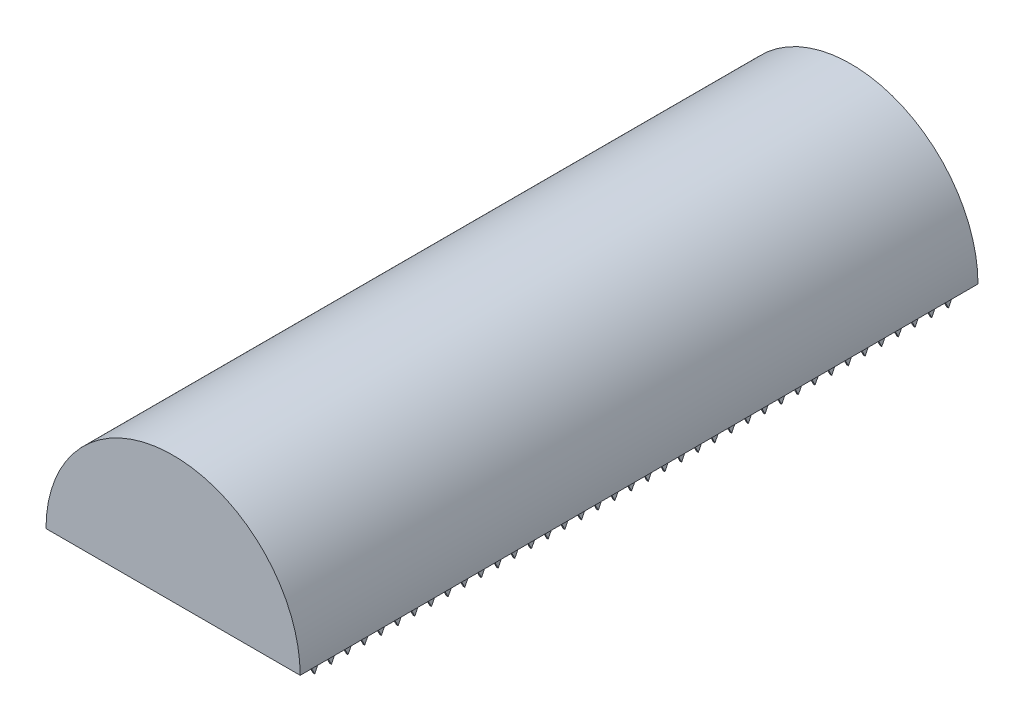
SolidWorks part; units mm, degrees
ref_plane "Front Plane" through (0, 0, 0) normal (0, 0, 1) x (1, 0, 0)
ref_plane "Top Plane" through (0, 0, 0) normal (0, 1, 0) x (1, 0, 0)
ref_plane "Right Plane" through (0, 0, 0) normal (1, 0, 0) x (0, 0, -1)
sketch "Sketch1" plane through (0, 0, 0) normal (0, 0, 1) x (1, 0, 0)
  line L0 (-76.2, 0) -> (76.2, 0)
  arc A0 (-76.2, 0) -> (76.2, 0) centre (0, 0) cw
  dimension "D1" = 76.2
extrude "Boss-Extrude1" add sketch "Sketch1" along normal blind 406.4
shell "Shell1" thickness 6.35
ref_plane "Plane1" through (69.85, 0, 0) normal (1, 0, 0) x (0, 0, -1)
sketch "Sketch3" plane through (69.85, 0, 0) normal (1, 0, 0) x (0, 0, -1)
  line L0 (-6.35, 0) -> (-11.35, -10)
  line L1 (-11.35, -10) -> (-16.35, 0)
  line L2 (-400.05, 0) -> (-6.35, 0) construction
  line L3 (-11.35, -10) -> (-11.35, 0) construction
  line L4 (-6.35, 0) -> (-16.35, 0) construction
  line L5 (-16.35, 0) -> (-21.35, -10)
  line L6 (-21.35, -10) -> (-26.35, 0)
  line L7 (-16.35, 0) -> (-26.35, 0) construction
  line L8 (-26.35, 0) -> (-31.35, -10)
  line L9 (-31.35, -10) -> (-36.35, 0)
  line L10 (-26.35, 0) -> (-36.35, 0) construction
  line L11 (-36.35, 0) -> (-41.35, -10)
  line L12 (-41.35, -10) -> (-46.35, 0)
  line L13 (-36.35, 0) -> (-46.35, 0) construction
  line L14 (-46.35, 0) -> (-51.35, -10)
  line L15 (-51.35, -10) -> (-56.35, 0)
  line L16 (-46.35, 0) -> (-56.35, 0) construction
  line L17 (-56.35, 0) -> (-61.35, -10)
  line L18 (-61.35, -10) -> (-66.35, 0)
  line L19 (-56.35, 0) -> (-66.35, 0) construction
  line L20 (-66.35, 0) -> (-71.35, -10)
  line L21 (-71.35, -10) -> (-76.35, 0)
  line L22 (-66.35, 0) -> (-76.35, 0) construction
  line L23 (-76.35, 0) -> (-81.35, -10)
  line L24 (-81.35, -10) -> (-86.35, 0)
  line L25 (-76.35, 0) -> (-86.35, 0) construction
  line L26 (-86.35, 0) -> (-91.35, -10)
  line L27 (-91.35, -10) -> (-96.35, 0)
  line L28 (-86.35, 0) -> (-96.35, 0) construction
  line L29 (-96.35, 0) -> (-101.35, -10)
  line L30 (-101.35, -10) -> (-106.35, 0)
  line L31 (-96.35, 0) -> (-106.35, 0) construction
  line L32 (-106.35, 0) -> (-111.35, -10)
  line L33 (-111.35, -10) -> (-116.35, 0)
  line L34 (-106.35, 0) -> (-116.35, 0) construction
  line L35 (-116.35, 0) -> (-121.35, -10)
  line L36 (-121.35, -10) -> (-126.35, 0)
  line L37 (-116.35, 0) -> (-126.35, 0) construction
  line L38 (-126.35, 0) -> (-131.35, -10)
  line L39 (-131.35, -10) -> (-136.35, 0)
  line L40 (-126.35, 0) -> (-136.35, 0) construction
  line L41 (-136.35, 0) -> (-141.35, -10)
  line L42 (-141.35, -10) -> (-146.35, 0)
  line L43 (-136.35, 0) -> (-146.35, 0) construction
  line L44 (-146.35, 0) -> (-151.35, -10)
  line L45 (-151.35, -10) -> (-156.35, 0)
  line L46 (-146.35, 0) -> (-156.35, 0) construction
  line L47 (-156.35, 0) -> (-161.35, -10)
  line L48 (-161.35, -10) -> (-166.35, 0)
  line L49 (-156.35, 0) -> (-166.35, 0) construction
  line L50 (-166.35, 0) -> (-171.35, -10)
  line L51 (-171.35, -10) -> (-176.35, 0)
  line L52 (-166.35, 0) -> (-176.35, 0) construction
  line L53 (-176.35, 0) -> (-181.35, -10)
  line L54 (-181.35, -10) -> (-186.35, 0)
  line L55 (-176.35, 0) -> (-186.35, 0) construction
  line L56 (-186.35, 0) -> (-191.35, -10)
  line L57 (-191.35, -10) -> (-196.35, 0)
  line L58 (-186.35, 0) -> (-196.35, 0) construction
  line L59 (-196.35, 0) -> (-201.35, -10)
  line L60 (-201.35, -10) -> (-206.35, 0)
  line L61 (-196.35, 0) -> (-206.35, 0) construction
  line L62 (-206.35, 0) -> (-211.35, -10)
  line L63 (-211.35, -10) -> (-216.35, 0)
  line L64 (-206.35, 0) -> (-216.35, 0) construction
  line L65 (-216.35, 0) -> (-221.35, -10)
  line L66 (-221.35, -10) -> (-226.35, 0)
  line L67 (-216.35, 0) -> (-226.35, 0) construction
  line L68 (-226.35, 0) -> (-231.35, -10)
  line L69 (-231.35, -10) -> (-236.35, 0)
  line L70 (-226.35, 0) -> (-236.35, 0) construction
  line L71 (-236.35, 0) -> (-241.35, -10)
  line L72 (-241.35, -10) -> (-246.35, 0)
  line L73 (-236.35, 0) -> (-246.35, 0) construction
  line L74 (-246.35, 0) -> (-251.35, -10)
  line L75 (-251.35, -10) -> (-256.35, 0)
  line L76 (-246.35, 0) -> (-256.35, 0) construction
  line L77 (-256.35, 0) -> (-261.35, -10)
  line L78 (-261.35, -10) -> (-266.35, 0)
  line L79 (-256.35, 0) -> (-266.35, 0) construction
  line L80 (-266.35, 0) -> (-271.35, -10)
  line L81 (-271.35, -10) -> (-276.35, 0)
  line L82 (-266.35, 0) -> (-276.35, 0) construction
  line L83 (-276.35, 0) -> (-281.35, -10)
  line L84 (-281.35, -10) -> (-286.35, 0)
  line L85 (-276.35, 0) -> (-286.35, 0) construction
  line L86 (-286.35, 0) -> (-291.35, -10)
  line L87 (-291.35, -10) -> (-296.35, 0)
  line L88 (-286.35, 0) -> (-296.35, 0) construction
  line L89 (-296.35, 0) -> (-301.35, -10)
  line L90 (-301.35, -10) -> (-306.35, 0)
  line L91 (-296.35, 0) -> (-306.35, 0) construction
  line L92 (-306.35, 0) -> (-311.35, -10)
  line L93 (-311.35, -10) -> (-316.35, 0)
  line L94 (-306.35, 0) -> (-316.35, 0) construction
  line L95 (-316.35, 0) -> (-321.35, -10)
  line L96 (-321.35, -10) -> (-326.35, 0)
  line L97 (-316.35, 0) -> (-326.35, 0) construction
  line L98 (-326.35, 0) -> (-331.35, -10)
  line L99 (-331.35, -10) -> (-336.35, 0)
  line L100 (-326.35, 0) -> (-336.35, 0) construction
  line L101 (-336.35, 0) -> (-341.35, -10)
  line L102 (-341.35, -10) -> (-346.35, 0)
  line L103 (-336.35, 0) -> (-346.35, 0) construction
  line L104 (-346.35, 0) -> (-351.35, -10)
  line L105 (-351.35, -10) -> (-356.35, 0)
  line L106 (-346.35, 0) -> (-356.35, 0) construction
  line L107 (-356.35, 0) -> (-361.35, -10)
  line L108 (-361.35, -10) -> (-366.35, 0)
  line L109 (-356.35, 0) -> (-366.35, 0) construction
  line L110 (-366.35, 0) -> (-371.35, -10)
  line L111 (-371.35, -10) -> (-376.35, 0)
  line L112 (-366.35, 0) -> (-376.35, 0) construction
  line L113 (-376.35, 0) -> (-381.35, -10)
  line L114 (-381.35, -10) -> (-386.35, 0)
  line L115 (-376.35, 0) -> (-386.35, 0) construction
  line L116 (-386.35, 0) -> (-391.35, -10)
  line L117 (-391.35, -10) -> (-396.35, 0)
  line L118 (-386.35, 0) -> (-396.35, 0) construction
  line L119 (-396.35, 0) -> (-6.35, 0)
  dimension "D1" = 10
  dimension "D2" = 10
  dimension "D3" = 39
extrude "Boss-Extrude2" add sketch "Sketch3" against normal blind 1 separate body contours L119 L1 L0 | L119 L6 L5 | L119 L9 L8 | L119 L12 L11 | L119 L15 L14 | L119 L18 L17 | L119 L21 L20 | L119 L24 L23 | L119 L27 L26 | L119 L30 L29 | L119 L33 L32 | L119 L36 L35 | L119 L39 L38 | L119 L42 L41 | L119 L45 L44 | L119 L48 L47 | L119 L51 L50 | L119 L54 L53 | L119 L57 L56 | L119 L60 L59 | L119 L63 L62 | L119 L66 L65 | L119 L69 L68 | L119 L72 L71 | L119 L75 L74 | L119 L78 L77 | L119 L81 L80 | L119 L84 L83 | L119 L87 L86 | L119 L90 L89 | L119 L93 L92 | L119 L96 L95 | L119 L99 L98 | L119 L117 L116 | L119 L114 L113 | L119 L111 L110 | L119 L108 L107 | L119 L105 L104 | L119 L102 L101
equation "\"1omm\"=9.38487"
